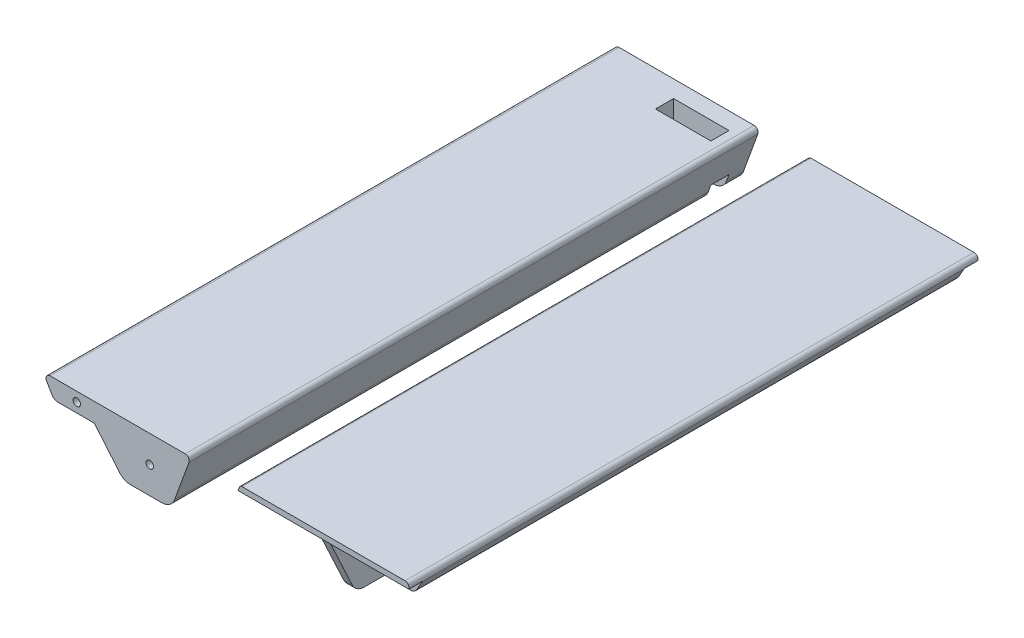
SolidWorks part; units mm, degrees
ref_plane "Front plane" through (0, 0, 0) normal (0, 0, 1) x (1, 0, 0)
ref_plane "Top plane" through (0, 0, 0) normal (0, 1, 0) x (1, 0, 0)
ref_plane "Right Plane" through (0, 0, 0) normal (1, 0, 0) x (0, 0, -1)
sketch "Sketch1" plane through (0, 0, 0) normal (0, 0, 1) x (1, 0, 0)
  line L0 (0, 0) -> (50, 0)
  line L1 (51.4095, -2.013) -> (44.8628, -20)
  line L2 (44.8628, -20) -> (27.295, -20)
  line L3 (27.295, -20) -> (16.3868, -7)
  line L5 (-1.299, -2.25) -> (0.7217, -5.75)
  line L6 (2.8868, -7) -> (16.3868, -7)
  line L8 (71, 0) -> (131.3335, 0)
  line L9 (132.6325, -2.25) -> (130.6118, -5.75)
  line L10 (100.6668, -2) -> (69.5719, -2)
  line L11 (100.6668, -2) -> (100.6668, -22)
  line L12 (100.6668, -22) -> (103.8168, -22)
  line L13 (70.0603, -0.658) -> (69.5719, -2)
  line L14 (103.8168, -22) -> (103.8168, -2)
  line L15 (103.8168, -2) -> (122.8168, -2)
  line L16 (122.8168, -2) -> (122.8168, -7)
  line L17 (122.8168, -7) -> (128.4468, -7)
  line L19 (123.8168, -2) -> (129.8168, -2)
  line L20 (123.8168, -2) -> (123.8168, -4.5)
  line L21 (123.8168, -4.5) -> (129.8168, -4.5)
  line L22 (129.8168, -2) -> (129.8168, -4.5)
  arc A0 (50, 0) -> (51.4095, -2.013) centre (50, -1.5) cw
  arc A1 (-1.299, -2.25) -> (0, 0) centre (0, -1.5) cw
  arc A2 (0.7217, -5.75) -> (2.8868, -7) centre (2.8868, -4.5) ccw
  arc A4 (131.3335, 0) -> (132.6325, -2.25) centre (131.3335, -1.5) cw
  arc A7 (128.4468, -7) -> (130.6118, -5.75) centre (128.4468, -4.5) ccw
  arc A8 (71, 0) -> (70.0603, -0.658) centre (71, -1) ccw
  dimension "D2" = 1.5
  dimension "D8" = 2.5
  dimension "D10" = 21
  dimension "D12" = 2.5
  dimension "D14" = 125.56
  dimension "D15" = 27.78
  dimension "D1" = 20
  dimension "D3" = 50
  dimension "D4" = 60
  dimension "D5" = 70
  dimension "D6" = 13.5
  dimension "D7" = 7
  dimension "D9" = 60
  dimension "D11" = 60
  dimension "D13" = 2
  dimension "D16" = 3.15
  dimension "D17" = 20
  dimension "D18" = 19
  dimension "D19" = 6
  dimension "D20" = 2.5
  dimension "D21" = 1
extrude "Boss-Extrude1" add sketch "Sketch1" along normal blind 105.25
sketch "Sketch2" plane through (0, 0, 105.25) normal (0, 0, 1) x (1, 0, 0)
  line L0 (9.8868, 0) -> (9.8868, -7) construction
  line L1 (50, 0) -> (0, 0) construction
  line L2 (2.8868, -7) -> (16.3868, -7) construction
  circle A0 centre (9.8868, -3.5) radius 1.375
  arc A1 (0.7217, -5.75) -> (2.8868, -7) centre (2.8868, -4.5) ccw construction
  circle A2 centre (36.8868, -10) radius 1.375
  dimension "D1" = 2.75
  dimension "D2" = 7
  dimension "D3" = 10
  dimension "D4" = 27
extrude "Cut-Extrude1" cut sketch "Sketch2" against normal blind 15
sketch "Sketch3" plane through (0, 0, 105.25) normal (0, 0, 1) x (1, 0, 0)
  line L0 (122.8168, -2) -> (132.7477, -2)
  line L1 (122.8168, -2) -> (122.8168, -7) construction
  line L2 (122.8168, -7) -> (128.4468, -7) construction
  line L3 (130.6118, -5.75) -> (132.6325, -2.25) construction
  line L4 (122.8168, -2) -> (122.8168, -7)
  line L5 (122.8168, -7) -> (128.4468, -7)
  line L6 (130.6118, -5.75) -> (132.6325, -2.25)
  arc A0 (128.4468, -7) -> (130.6118, -5.75) centre (128.4468, -4.5) ccw construction
  arc A1 (132.6325, -2.25) -> (131.3335, 0) centre (131.3335, -1.5) ccw construction
  arc A2 (128.4468, -7) -> (130.6118, -5.75) centre (128.4468, -4.5) ccw
  arc A3 (132.6325, -2.25) -> (132.7477, -2) centre (131.3335, -1.5) ccw
extrude "Cut-Extrude2" cut sketch "Sketch3" against normal blind 5
mirror "Mirror1" about plane through (0, -1.5, 0) normal (0, 0, -1) of bodies 104 107 103
fillet "Fillet1" radius 5 2 edges at (44.8628, -20, 0) (27.295, -20, 0)
sketch "Sketch4" plane through (103.8168, 0, 0) normal (1, 0, 0) x (0, 0, -1)
  line L0 (-105.25, -22) -> (-105.25, -2)
  line L1 (-105.25, -2) -> (-95.9238, -22)
  line L2 (-105.25, -22) -> (105.25, -22) construction
  line L3 (-95.9238, -22) -> (-105.25, -22)
  line L4 (105.25, -2) -> (90.25, -2)
  line L5 (-105.25, -2) -> (105.25, -2) construction
  line L6 (90.25, -2) -> (80.9238, -22)
  line L7 (80.9238, -22) -> (105.25, -22)
  line L8 (105.25, -22) -> (105.25, -2)
  line L9 (-100.25, -2) -> (-105.25, -2) construction
  circle A0 centre (-81.25, -17) radius 1.375
  circle A1 centre (-61.25, -17) radius 1.375
  circle A2 centre (-41.25, -17) radius 1.375
  circle A3 centre (-21.25, -17) radius 1.375
  circle A4 centre (-1.25, -17) radius 1.375
  circle A5 centre (18.75, -17) radius 1.375
  circle A6 centre (38.75, -17) radius 1.375
  circle A7 centre (58.75, -17) radius 1.375
  circle A8 centre (78.75, -17) radius 1.375
  dimension "D5" = 2.75
  dimension "D8" = 20
  dimension "D1" = 25
  dimension "D2" = 25
  dimension "D3" = 15
  dimension "D4" = 24
  dimension "D6" = 15
  dimension "D7" = 9
extrude "Cut-Extrude3" cut sketch "Sketch4" against normal up to vertex (3.15 mm away)
fillet "Fillet2" radius 5 2 edges at (102.2418, -22, 95.9238) (102.2418, -22, -80.9238)
sketch "Sketch5" plane through (0, 0, 0) normal (0, 1, 0) x (1, 0, 0)
  line L0 (50, 105.25) -> (0, 105.25) construction
  line L1 (47, 98.95) -> (26.5, 98.95)
  line L2 (47, 98.95) -> (47, 92.25)
  line L3 (47, 92.25) -> (26.5, 92.25)
  line L4 (26.5, 98.95) -> (26.5, 92.25)
  dimension "D1" = 20.5
  dimension "D2" = 6.7
  dimension "D3" = 13
  dimension "D4" = 47
extrude "Cut-Extrude4" cut sketch "Sketch5" against normal through all
sketch "Sketch6" plane through (0, 0, -105.25) normal (0, 0, -1) x (-1, 0, 0)
  line L0 (-41.5, -11.2) -> (-32, -11.2) construction
  line L1 (-26.5, 0) -> (-47, 0) construction
  line L2 (-50, 0) -> (0, 0) construction
  circle A0 centre (-41.5, -11.2) radius 1.125
  circle A1 centre (-32, -11.2) radius 1.125
  point P4 (-36.75, 0)
  point P5 (-36.75, -11.2)
  dimension "D3" = 2.25
  dimension "D1" = 11.2
  dimension "D2" = 9.5
extrude "Cut-Extrude5" cut sketch "Sketch6" against normal blind 20
sketch "Sketch7" plane through (0, 0, -105.25) normal (0, 0, -1) x (-1, 0, 0)
  circle A0 centre (-41.5, -11.2) radius 2.5
  circle A1 centre (-32, -11.2) radius 2.5
  dimension "D1" = 5
extrude "Cut-Extrude6" cut sketch "Sketch7" against normal up to vertex
